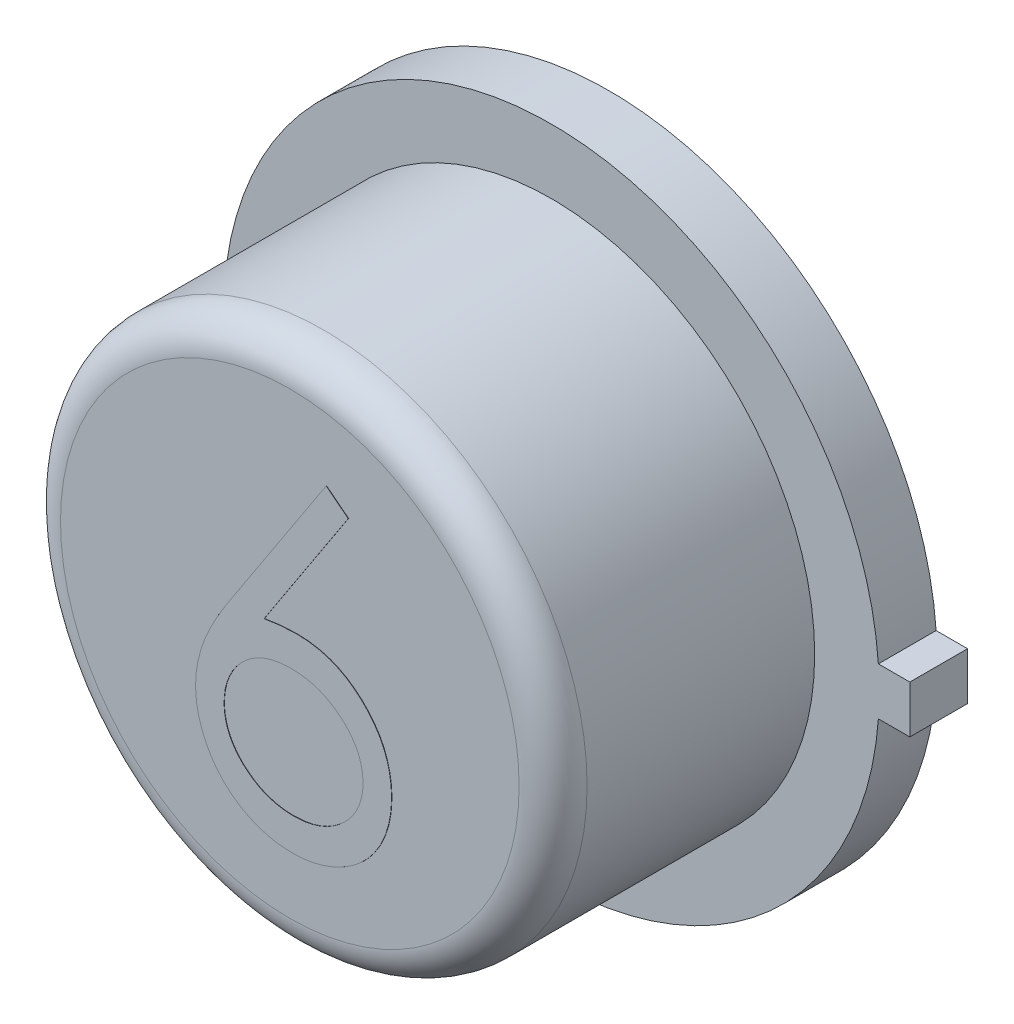
SolidWorks part; units mm, degrees
ref_plane "Front Plane" through (0, 0, 0) normal (0, 0, 1) x (1, 0, 0)
ref_plane "Top Plane" through (0, 0, 0) normal (0, 1, 0) x (1, 0, 0)
ref_plane "Right Plane" through (0, 0, 0) normal (1, 0, 0) x (0, 0, -1)
sketch "Sketch1" plane through (0, 0, 0) normal (0, 0, 1) x (1, 0, 0)
  line L1 (2.4511, 0.1778) -> (2.6797, 0.1778)
  line L3 (2.4511, -0.1778) -> (2.6797, -0.1778)
  line L4 (2.6797, 0.1778) -> (2.6797, -0.1778)
  line L5 (2.4511, 0.1778) -> (2.4444, 0.1778)
  line L6 (2.4511, -0.1778) -> (2.4446, -0.1778)
  arc A0 (2.4446, 0.1778) -> (2.4446, -0.1778) centre (0, 0) ccw
  dimension "D1" = 4.9022
  dimension "D2" = 0.3556
  dimension "D3" = 0.2286
extrude "Boss-Extrude1" add sketch "Sketch1" along normal blind 0.4318
sketch "Sketch2" plane through (0, 0, 0.4318) normal (0, 0, 1) x (1, 0, 0)
  circle A0 centre (0, 0) radius 1.9685
  dimension "D1" = 3.937
extrude "Boss-Extrude2" add sketch "Sketch2" along normal blind 1.9558
sketch "Sketch3" plane through (0, 0, 0) normal (0, 0, -1) x (-1, 0, 0)
  circle A0 centre (0, 0) radius 1.7576
extrude "Boss-Extrude3" add sketch "Sketch3" along normal blind 0.0025
fillet "Fillet1" radius 0.254 1 edges at (1.9685, 0, 2.3876)
sketch "Sketch4" plane through (0, 0, 2.3876) normal (0, 0, 1) x (1, 0, 0)
  line L0 (-1.2065, -1.2181) -> (1.2065, -1.2181) construction
  circle A0 centre (0, 0) radius 1.7145 construction
  text T0 "6" font "Century Gothic" height in points 9
  dimension "D1" = 2.413
extrude "Boss-Extrude6" add sketch "Sketch4" along normal blind 0.0025
